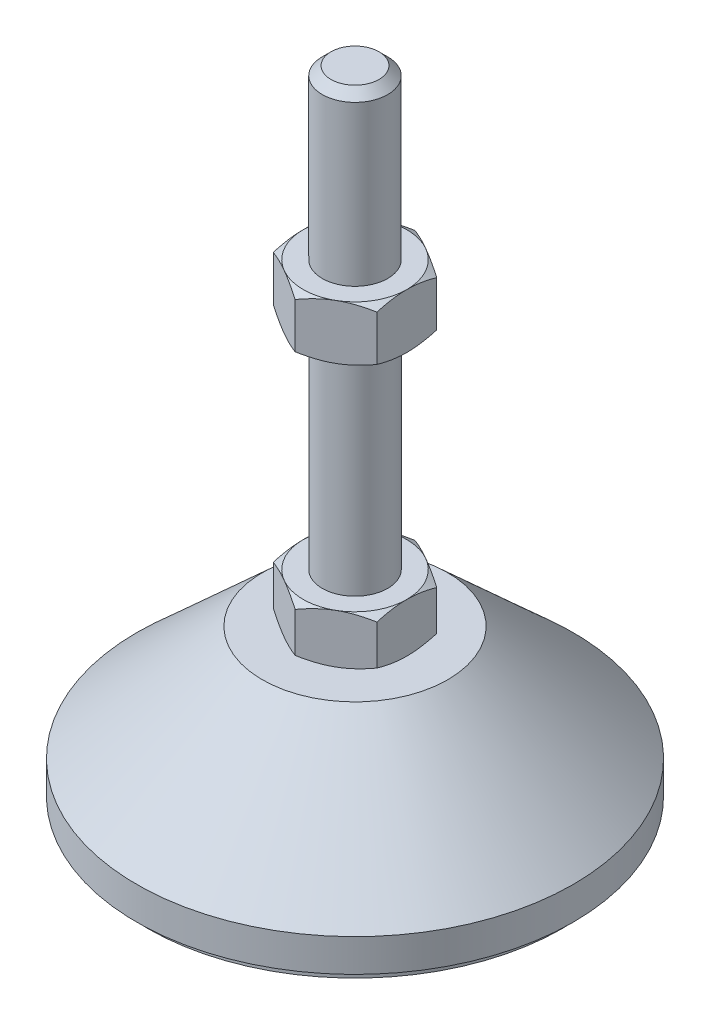
SolidWorks part; units mm, degrees
ref_plane "Спереди" through (0, 0, 0) normal (0, 0, 1) x (1, 0, 0)
ref_plane "Сверху" through (0, 0, 0) normal (0, 1, 0) x (1, 0, 0)
ref_plane "Справа" through (0, 0, 0) normal (1, 0, 0) x (0, 0, -1)
sketch "Эскиз1" plane through (0, 0, 0) normal (0, 0, 1) x (1, 0, 0)
  line L0 (0, 0) -> (-38, 0)
  line L1 (-38, 0) -> (-38, 2)
  line L2 (-38, 2) -> (-40, 2)
  line L3 (-40, 2) -> (-40, 8)
  line L4 (-40, 8) -> (-17, 29)
  line L5 (-17, 29) -> (-6, 29)
  line L12 (-6, 38) -> (-6, 116.4)
  line L13 (-6, 116.4) -> (-4.4, 118)
  line L14 (-4.4, 118) -> (0, 118)
  line L15 (0, 118) -> (0, 0) construction
  line L16 (-6, 29) -> (0, 29) construction
  line L17 (0, 0) -> (0, 118)
  line L18 (0, 0) -> (0, -7.9595) construction
  line L19 (-6, 38) -> (-6, 29)
  point P8 (-6, 77.2)
  point P23 (-11.5, 29)
  dimension "D1" = 12
  dimension "D2" = 29
  dimension "D3" = 9
  dimension "D4" = 80
  dimension "D5" = 6
  dimension "D6" = 1.6
  dimension "D7" = 45
  dimension "D8" = 34
  dimension "D9" = 2
  dimension "D10" = 80
  dimension "D11" = 6
revolve "Повернуть1" add sketch "Эскиз1" angle 360 about L17
sketch "Эскиз2" plane through (0, 29, 0) normal (0, 1, 0) x (1, 0, 0)
  line L1 (0, 10.9697) -> (-9.5, 5.4848)
  line L2 (-9.5, 5.4848) -> (-9.5, -5.4848)
  line L3 (-9.5, -5.4848) -> (0, -10.9697)
  line L4 (0, -10.9697) -> (9.5, -5.4848)
  line L5 (9.5, -5.4848) -> (9.5, 5.4848)
  line L6 (9.5, 5.4848) -> (0, 10.9697)
  circle A0 centre (0, 0) radius 9.5 construction
  dimension "D1" = 19
extrude "Бобышка-Вытянуть1" add sketch "Эскиз2" along normal up to vertex (9 mm away) up to point (-6, 38, 0)
ref_plane "Плоскость1" through (0, 77.2, 0) normal (0, 1, 0) x (1, 0, 0)
sketch "Эскиз3" plane through (0, 77.2, 0) normal (0, 1, 0) x (1, 0, 0)
  line L6 (9.5, 5.4848) -> (0, 10.9697)
  line L7 (0, 10.9697) -> (-9.5, 5.4848)
  line L8 (-9.5, 5.4848) -> (-9.5, -5.4848)
  line L9 (-9.5, -5.4848) -> (0, -10.9697)
  line L10 (0, -10.9697) -> (9.5, -5.4848)
  line L11 (9.5, -5.4848) -> (9.5, 5.4848)
  line L12 (9.5, 5.4848) -> (0, 10.9697)
  line L13 (0, 10.9697) -> (-9.5, 5.4848)
  line L14 (-9.5, 5.4848) -> (-9.5, -5.4848)
  line L15 (-9.5, -5.4848) -> (0, -10.9697)
  line L16 (0, -10.9697) -> (9.5, -5.4848)
  line L17 (9.5, -5.4848) -> (9.5, 5.4848)
  dimension "D1" = 0
extrude "Бобышка-Вытянуть2" add sketch "Эскиз3" along normal blind 10
sketch "Эскиз4" plane through (0, 0, 0) normal (0, 0, 1) x (1, 0, 0)
  line L0 (-9.5, 87.2) -> (-18.1603, 82.2)
  line L1 (-18.1603, 82.2) -> (-18.1603, 87.2)
  line L2 (-18.1603, 87.2) -> (-9.5, 87.2)
  line L3 (-18.1603, 82.2) -> (-9.5, 77.2)
  line L4 (50, 77.2) -> (-50, 77.2) construction
  line L5 (-9.5, 77.2) -> (-18.1603, 77.2)
  line L6 (-18.1603, 77.2) -> (-18.1603, 82.2)
  line L7 (-9.5, 87.2) -> (-9.5, 77.2) construction
  line L8 (-9.5, 38) -> (-17.2942, 38)
  line L9 (-17.2942, 38) -> (-17.2942, 33.5)
  line L10 (-17.2942, 33.5) -> (-9.5, 38)
  line L11 (-9.5, 29) -> (-17.2942, 33.5)
  line L12 (-17.2942, 33.5) -> (-17.2942, 29)
  line L13 (-17.2942, 29) -> (-9.5, 29)
  line L14 (0, 118) -> (0, 96.3793) construction
  dimension "D1" = 30
  dimension "D2" = 30
revolve "Вырез-Повернуть2" cut sketch "Эскиз4" angle 360 about L14
